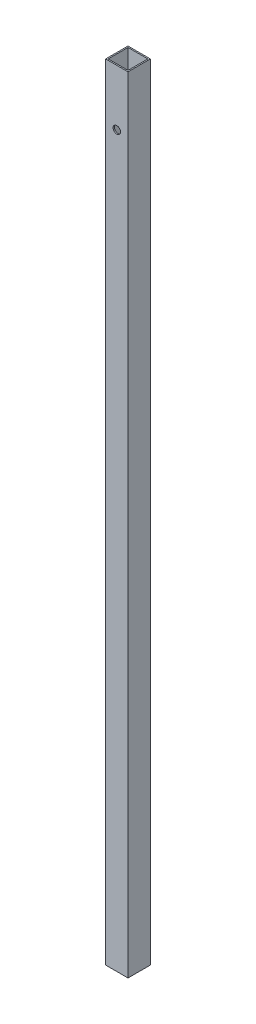
SolidWorks part; units mm, degrees
ref_plane "Front Plane" through (0, 0, 0) normal (0, 0, 1) x (1, 0, 0)
ref_plane "Top Plane" through (0, 0, 0) normal (0, 1, 0) x (1, 0, 0)
ref_plane "Right Plane" through (0, 0, 0) normal (1, 0, 0) x (0, 0, -1)
sketch "Sketch1" plane through (0, 0, 0) normal (0, 1, 0) x (1, 0, 0)
  line L0 (-8, 8) -> (-8, -8)
  line L1 (-9, 9) -> (9, 9)
  line L2 (-9, 9) -> (-9, -9)
  line L3 (-9, -9) -> (9, -9)
  line L4 (9, 9) -> (9, -9)
  line L5 (-9, 9) -> (9, -9) construction
  line L6 (-9, -9) -> (9, 9) construction
  line L7 (-8, -8) -> (8, -8)
  line L8 (8, 8) -> (8, -8)
  line L9 (-8, 8) -> (8, 8)
  point P0 (0, 0)
  dimension "D1" = 18
  dimension "D2" = 18
  dimension "D3" = 1
extrude "Boss-Extrude1" add sketch "Sketch1" along normal blind 632
sketch "Sketch2" plane through (0, 0, 9) normal (0, 0, 1) x (1, 0, 0)
  line L0 (-9, 632) -> (9, 632) construction
  line L1 (-9, 632) -> (-9, 0) construction
  circle A0 centre (0, 587) radius 3
  dimension "D1" = 6
  dimension "D2" = 45
  dimension "D3" = 9
extrude "Cut-Extrude1" cut sketch "Sketch2" against normal blind 993
